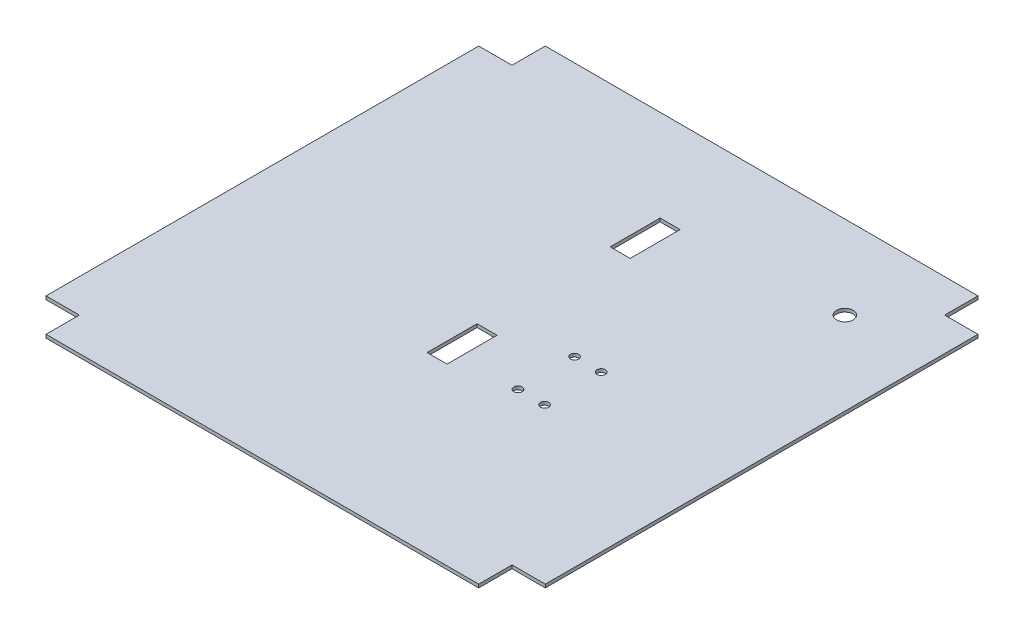
SolidWorks part; units mm, degrees
material "St.37"
ref_plane "Front Plane" through (0, 0, 0) normal (0, 0, 1) x (1, 0, 0)
ref_plane "Top Plane" through (0, 0, 0) normal (0, 1, 0) x (1, 0, 0)
ref_plane "Right Plane" through (0, 0, 0) normal (1, 0, 0) x (0, 0, -1)
sketch "Sketch1" plane through (0, 0, 0) normal (0, 1, 0) x (1, 0, 0)
  line L0 (-130, 150) -> (-130, 130)
  line L1 (-130, 150) -> (130, 150)
  line L2 (-150, 130) -> (-150, -130)
  line L3 (-130, -150) -> (130, -150)
  line L4 (150, 130) -> (150, -130)
  line L5 (-130, 130) -> (130, -130) construction
  line L6 (-130, -130) -> (130, 130) construction
  line L7 (-130, 130) -> (-150, 130)
  line L8 (-150, -130) -> (-130, -130)
  line L9 (-130, -130) -> (-130, -150)
  line L10 (130, 150) -> (130, 130)
  line L11 (130, 130) -> (150, 130)
  line L12 (150, -130) -> (130, -130)
  line L13 (130, -130) -> (130, -150)
  point P0 (0, 0)
  dimension "D1" = 150
  dimension "D2" = 20
extrude "Boss-Extrude1" add sketch "Sketch1" along normal blind 2
sketch "Sketch2" plane through (0, 2, 0) normal (0, 1, 0) x (1, 0, 0)
  line L0 (-130, -150) -> (130, -150) construction
  line L1 (6, -45) -> (-6, -45)
  line L2 (6, -45) -> (6, -15)
  line L3 (6, -15) -> (-6, -15)
  line L4 (-6, -45) -> (-6, -15)
  line L5 (6, -45) -> (-6, -15) construction
  line L6 (6, -15) -> (-6, -45) construction
  line L7 (6, 65) -> (6, 95)
  line L8 (6, 65) -> (-6, 65)
  line L9 (-6, 65) -> (-6, 95)
  line L10 (6, 95) -> (-6, 95)
  line L11 (150, 130) -> (130, 130) construction
  line L12 (130, 130) -> (130, 150) construction
  line L14 (150, -130) -> (150, 130) construction
  line L15 (130, 150) -> (-130, 150) construction
  circle A0 centre (100, 100) radius 5
  circle A1 centre (56.45, -2.85) radius 2.5
  circle A2 centre (40.45, -2.85) radius 2.5
  circle A3 centre (40.45, -36.85) radius 2.5
  circle A4 centre (56.45, -36.85) radius 2.5
  point P0 (0, -30)
  dimension "D6" = 30
  dimension "D8" = 10
  dimension "D11" = 5
  dimension "D15" = 34
  dimension "D16" = 16
  dimension "D1" = 12
  dimension "D2" = 30
  dimension "D3" = 120
  dimension "D5" = 80
  dimension "D7" = 30
  dimension "D9" = 93.55
  dimension "D10" = 152.85
  dimension "D13" = 16
  dimension "D4" = 2
  dimension "D14" = 2
  dimension "D12" = 2
extrude "Cut-Extrude1" cut sketch "Sketch2" against normal blind 10
